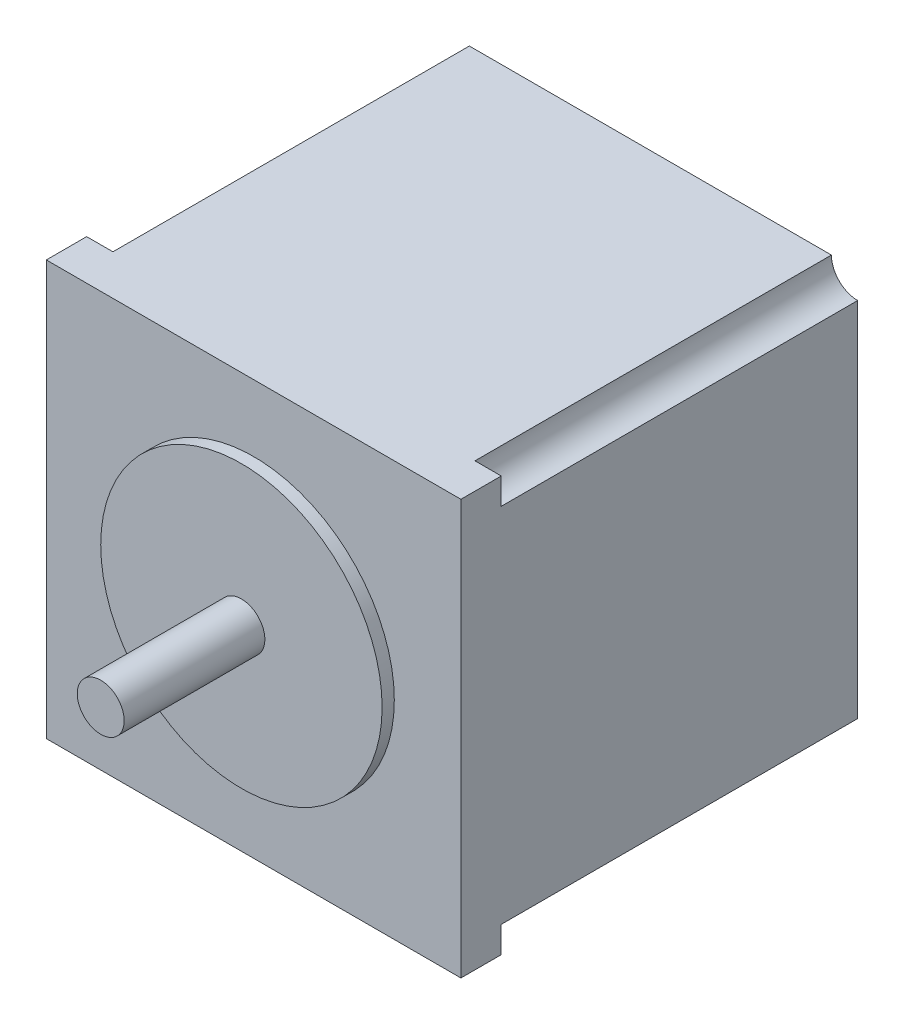
SolidWorks part; units mm, degrees
ref_plane "Front Plane" through (0, 0, 0) normal (0, 0, 1) x (1, 0, 0)
ref_plane "Top Plane" through (0, 0, 0) normal (0, 1, 0) x (1, 0, 0)
ref_plane "Right Plane" through (0, 0, 0) normal (1, 0, 0) x (0, 0, -1)
sketch "Sketch2" plane through (0, 0, 0) normal (0, 0, 1) x (1, 0, 0)
  line L1 (0, 0) -> (56.134, 0)
  line L2 (0, 0) -> (0, 56.134)
  line L3 (0, 56.134) -> (56.134, 56.134)
  line L4 (56.134, 0) -> (56.134, 56.134)
  dimension "D1" = 56.134
  dimension "D2" = 56.134
extrude "Boss-Extrude1" add sketch "Sketch2" along normal blind 5.461
sketch "Sketch3" plane through (0, 0, 5.461) normal (0, 0, 1) x (1, 0, 0)
  circle A0 centre (28.067, 28.067) radius 19.05
extrude "Boss-Extrude2" add sketch "Sketch3" along normal blind 1.651
sketch "Sketch4" plane through (0, 0, 0) normal (0, 0, -1) x (-1, 0, 0)
  line L0 (-56.134, 56.134) -> (0, 56.134) construction
  line L5 (-52.578, 56.134) -> (-3.556, 56.134)
  line L6 (-56.134, 52.578) -> (-56.134, 3.556)
  line L7 (-52.578, 0) -> (-3.556, 0)
  line L8 (0, 52.578) -> (0, 3.556)
  arc A0 (-56.134, 52.578) -> (-52.578, 56.134) centre (-56.134, 56.134) ccw
  arc A1 (-3.556, 56.134) -> (0, 52.578) centre (0, 56.134) ccw
  arc A2 (0, 3.556) -> (-3.556, 0) centre (0, 0) ccw
  arc A3 (-52.578, 0) -> (-56.134, 3.556) centre (-56.134, 0) ccw
  point P0 (-28.067, 28.067)
extrude "Boss-Extrude3" add sketch "Sketch4" along normal blind 48.26
sketch "Sketch5" plane through (0, 0, 7.112) normal (0, 0, 1) x (1, 0, 0)
  circle A0 centre (28.067, 28.067) radius 3.175
extrude "Boss-Extrude4" add sketch "Sketch5" along normal blind 19.05
